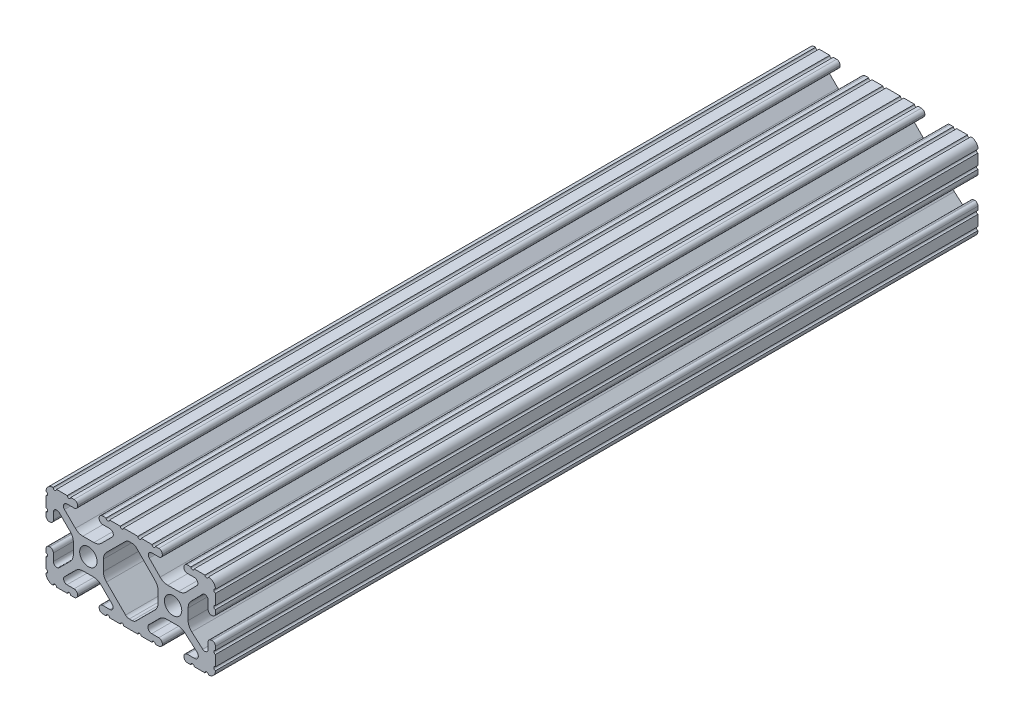
SolidWorks part; units mm, degrees
ref_plane "Front Plane" through (0, 0, 0) normal (0, 0, 1) x (1, 0, 0)
ref_plane "Top Plane" through (0, 0, 0) normal (0, 1, 0) x (1, 0, 0)
ref_plane "Right Plane" through (0, 0, 0) normal (1, 0, 0) x (0, 0, -1)
sketch "Sketch1" plane through (0, 0, 0) normal (0, 0, 1) x (1, 0, 0)
  line L0 (-7.2595, -3.8694) -> (-1.5457, -9.5728)
  line L1 (-8.1915, 1.6223) -> (-8.1915, -1.6223)
  line L2 (-1.504, 9.5765) -> (-7.252, 3.8768)
  line L3 (0.5515, 10.033) -> (-0.3952, 10.033)
  line L4 (7.2829, 3.8459) -> (1.6756, 9.5611)
  line L5 (8.1915, -1.6223) -> (8.1915, 1.6223)
  line L6 (1.5457, -9.5728) -> (7.2595, -3.8694)
  line L7 (-0.4332, -10.033) -> (0.4332, -10.033)
  line L8 (18.0171, 12.7) -> (16.9875, 12.7)
  line L9 (15.9385, 11.651) -> (15.9385, 11.5392)
  line L10 (16.9875, 10.4902) -> (19.1164, 10.4902)
  line L11 (19.8441, 8.7652) -> (16.619, 5.4551)
  line L12 (14.3449, 4.4958) -> (11.0833, 4.4958)
  line L13 (8.817, 5.4472) -> (5.5642, 8.7627)
  line L14 (6.2894, 10.4902) -> (8.4125, 10.4902)
  line L15 (9.4615, 11.5392) -> (9.4615, 11.651)
  line L16 (8.4125, 12.7) -> (7.3829, 12.7)
  line L17 (6.3669, 12.7) -> (3.1496, 12.7)
  line L18 (2.1336, 12.7) -> (-2.1336, 12.7)
  line L19 (-3.1496, 12.7) -> (-6.3669, 12.7)
  line L20 (-7.3829, 12.7) -> (-8.4125, 12.7)
  line L21 (-9.4615, 11.651) -> (-9.4615, 11.5392)
  line L22 (-8.4125, 10.4902) -> (-6.2836, 10.4902)
  line L23 (-5.5326, 8.6661) -> (-8.81, 5.4163)
  line L24 (-11.0455, 4.4958) -> (-14.3545, 4.4958)
  line L25 (-16.59, 5.4163) -> (-19.8674, 8.6661)
  line L26 (-19.1164, 10.4902) -> (-16.9875, 10.4902)
  line L27 (-15.9385, 11.5392) -> (-15.9385, 11.651)
  line L28 (-16.9875, 12.7) -> (-18.0171, 12.7)
  line L29 (-19.0331, 12.7) -> (-22.2504, 12.7)
  line L30 (-25.4, 9.5504) -> (-25.4, 6.3331)
  line L31 (-25.4, 5.3171) -> (-25.4, 4.2375)
  line L32 (-24.401, 3.2385) -> (-24.2392, 3.2385)
  line L33 (-23.1902, 4.2875) -> (-23.1902, 6.3347)
  line L34 (-21.434, 7.0665) -> (-18.148, 3.8082)
  line L35 (-17.2085, 1.5536) -> (-17.2085, -1.6952)
  line L36 (-18.1405, -3.9423) -> (-21.4316, -7.2274)
  line L37 (-23.1902, -6.498) -> (-23.1902, -4.2875)
  line L38 (-24.2392, -3.2385) -> (-24.351, -3.2385)
  line L39 (-25.4, -4.2875) -> (-25.4, -5.3171)
  line L40 (-25.4, -6.3331) -> (-25.4, -9.5504)
  line L41 (-22.2504, -12.7) -> (-19.0331, -12.7)
  line L42 (-18.0171, -12.7) -> (-16.9875, -12.7)
  line L43 (-15.9384, -11.651) -> (-15.9384, -11.5392)
  line L44 (-16.9875, -10.4902) -> (-19.1164, -10.4902)
  line L45 (-19.8341, -8.7551) -> (-16.4966, -5.4237)
  line L46 (-14.2536, -4.4958) -> (-11.1464, -4.4958)
  line L47 (-8.9034, -5.4237) -> (-5.5659, -8.7551)
  line L48 (-6.2836, -10.4902) -> (-8.4125, -10.4902)
  line L49 (-9.4616, -11.5392) -> (-9.4616, -11.651)
  line L50 (-8.4125, -12.7) -> (-7.3829, -12.7)
  line L51 (-6.3669, -12.7) -> (-3.1496, -12.7)
  line L52 (-2.1336, -12.7) -> (2.1336, -12.7)
  line L53 (3.1496, -12.7) -> (6.3669, -12.7)
  line L54 (7.3829, -12.7) -> (8.4125, -12.7)
  line L55 (9.4616, -11.651) -> (9.4616, -11.5392)
  line L56 (8.4125, -10.4902) -> (6.2894, -10.4902)
  line L57 (5.4807, -8.5353) -> (8.5979, -5.4237)
  line L58 (10.8409, -4.4958) -> (14.1026, -4.4958)
  line L59 (16.1879, -5.2766) -> (19.8682, -8.4822)
  line L60 (19.1164, -10.4902) -> (16.9875, -10.4902)
  line L61 (15.9384, -11.5392) -> (15.9384, -11.651)
  line L62 (16.9875, -12.7) -> (18.0171, -12.7)
  line L63 (19.0331, -12.7) -> (22.2504, -12.7)
  line L64 (25.4, -9.5504) -> (25.4, -6.3331)
  line L65 (25.4, -5.3171) -> (25.4, -4.2375)
  line L66 (24.401, -3.2385) -> (24.1892, -3.2385)
  line L67 (23.1902, -4.2375) -> (23.1902, -6.1559)
  line L68 (21.584, -6.8869) -> (18.2982, -4.025)
  line L69 (17.2085, -1.6308) -> (17.2085, 1.6308)
  line L70 (18.1094, 3.8465) -> (21.5263, 7.3534)
  line L71 (23.1902, 6.6769) -> (23.1902, 4.2375)
  line L72 (24.1892, 3.2385) -> (24.401, 3.2385)
  line L73 (25.4, 4.2375) -> (25.4, 5.3171)
  line L74 (25.4, 6.3332) -> (25.4, 9.5504)
  line L75 (22.2504, 12.7) -> (19.0331, 12.7)
  circle A0 centre (-12.7, 0) radius 2.6035
  circle A1 centre (12.7, 0) radius 2.6035
  arc A2 (-1.5457, -9.5728) -> (-0.4332, -10.033) centre (-0.4332, -8.4582) ccw
  arc A3 (-8.1915, -1.6223) -> (-7.2595, -3.8694) centre (-5.0165, -1.6223) ccw
  arc A4 (-7.252, 3.8768) -> (-8.1915, 1.6223) centre (-5.0165, 1.6223) ccw
  arc A5 (-0.3952, 10.033) -> (-1.504, 9.5765) centre (-0.3952, 8.4582) ccw
  arc A6 (1.6756, 9.5611) -> (0.5515, 10.033) centre (0.5515, 8.4582) ccw
  arc A7 (8.1915, 1.6223) -> (7.2829, 3.8459) centre (5.0165, 1.6223) ccw
  arc A8 (7.2595, -3.8694) -> (8.1915, -1.6223) centre (5.0165, -1.6223) ccw
  arc A9 (0.4332, -10.033) -> (1.5457, -9.5728) centre (0.4332, -8.4582) ccw
  arc A10 (18.0171, 12.7) -> (19.0331, 12.7) centre (18.5251, 12.7) ccw
  arc A11 (16.9875, 12.7) -> (15.9385, 11.651) centre (16.9875, 11.651) ccw
  arc A12 (15.9385, 11.5392) -> (16.9875, 10.4902) centre (16.9875, 11.5392) ccw
  arc A13 (19.8441, 8.7652) -> (19.1164, 10.4902) centre (19.1164, 9.4742) ccw
  arc A14 (14.3449, 4.4958) -> (16.619, 5.4551) centre (14.3449, 7.6708) ccw
  arc A15 (8.817, 5.4472) -> (11.0833, 4.4958) centre (11.0833, 7.6708) ccw
  arc A16 (6.2894, 10.4902) -> (5.5642, 8.7627) centre (6.2894, 9.4742) ccw
  arc A17 (8.4125, 10.4902) -> (9.4615, 11.5392) centre (8.4125, 11.5392) ccw
  arc A18 (9.4615, 11.651) -> (8.4125, 12.7) centre (8.4125, 11.651) ccw
  arc A19 (6.3669, 12.7) -> (7.3829, 12.7) centre (6.8749, 12.7) ccw
  arc A20 (2.1336, 12.7) -> (3.1496, 12.7) centre (2.6416, 12.7) ccw
  arc A21 (-3.1496, 12.7) -> (-2.1336, 12.7) centre (-2.6416, 12.7) ccw
  arc A22 (-7.3829, 12.7) -> (-6.3669, 12.7) centre (-6.8749, 12.7) ccw
  arc A23 (-8.4125, 12.7) -> (-9.4615, 11.651) centre (-8.4125, 11.651) ccw
  arc A24 (-9.4615, 11.5392) -> (-8.4125, 10.4902) centre (-8.4125, 11.5392) ccw
  arc A25 (-5.5326, 8.6661) -> (-6.2836, 10.4902) centre (-6.2836, 9.4235) ccw
  arc A26 (-11.0455, 4.4958) -> (-8.81, 5.4163) centre (-11.0455, 7.6708) ccw
  arc A27 (-16.59, 5.4163) -> (-14.3545, 4.4958) centre (-14.3545, 7.6708) ccw
  arc A28 (-19.1164, 10.4902) -> (-19.8674, 8.6661) centre (-19.1164, 9.4235) ccw
  arc A29 (-16.9875, 10.4902) -> (-15.9385, 11.5392) centre (-16.9875, 11.5392) ccw
  arc A30 (-15.9385, 11.651) -> (-16.9875, 12.7) centre (-16.9875, 11.651) ccw
  arc A31 (-19.0331, 12.7) -> (-18.0171, 12.7) centre (-18.5251, 12.7) ccw
  arc A32 (-23.2664, 12.6998) -> (-22.2504, 12.7) centre (-22.7584, 12.7) ccw
  arc A33 (-23.2664, 12.6998) -> (-25.3998, 10.5664) centre (-23.2918, 10.5918) ccw
  arc A34 (-25.4, 9.5504) -> (-25.3998, 10.5664) centre (-25.4, 10.0584) ccw
  arc A35 (-25.4, 5.3171) -> (-25.4, 6.3331) centre (-25.4, 5.8251) ccw
  arc A36 (-25.4, 4.2375) -> (-24.401, 3.2385) centre (-24.401, 4.2375) ccw
  arc A37 (-24.2392, 3.2385) -> (-23.1902, 4.2875) centre (-24.2392, 4.2875) ccw
  arc A38 (-21.434, 7.0665) -> (-23.1902, 6.3347) centre (-22.1596, 6.3347) ccw
  arc A39 (-17.2085, 1.5536) -> (-18.148, 3.8082) centre (-20.3835, 1.5536) ccw
  arc A40 (-18.1405, -3.9423) -> (-17.2085, -1.6952) centre (-20.3835, -1.6952) ccw
  arc A41 (-23.1902, -6.498) -> (-21.4316, -7.2274) centre (-22.1596, -6.498) ccw
  arc A42 (-23.1902, -4.2875) -> (-24.2392, -3.2385) centre (-24.2392, -4.2875) ccw
  arc A43 (-24.351, -3.2385) -> (-25.4, -4.2875) centre (-24.351, -4.2875) ccw
  arc A44 (-25.4, -6.3331) -> (-25.4, -5.3171) centre (-25.4, -5.8251) ccw
  arc A45 (-25.3998, -10.5664) -> (-25.4, -9.5504) centre (-25.4, -10.0584) ccw
  arc A46 (-25.3998, -10.5664) -> (-23.2664, -12.6998) centre (-23.2918, -10.5918) ccw
  arc A47 (-22.2504, -12.7) -> (-23.2664, -12.6998) centre (-22.7584, -12.7) ccw
  arc A48 (-18.0171, -12.7) -> (-19.0331, -12.7) centre (-18.5251, -12.7) ccw
  arc A49 (-16.9875, -12.7) -> (-15.9384, -11.651) centre (-16.9875, -11.651) ccw
  arc A50 (-15.9384, -11.5392) -> (-16.9875, -10.4902) centre (-16.9875, -11.5392) ccw
  arc A51 (-19.8341, -8.7551) -> (-19.1164, -10.4902) centre (-19.1164, -9.4742) ccw
  arc A52 (-14.2536, -4.4958) -> (-16.4966, -5.4237) centre (-14.2536, -7.6708) ccw
  arc A53 (-8.9034, -5.4237) -> (-11.1464, -4.4958) centre (-11.1464, -7.6708) ccw
  arc A54 (-6.2836, -10.4902) -> (-5.5659, -8.7551) centre (-6.2836, -9.4742) ccw
  arc A55 (-8.4125, -10.4902) -> (-9.4616, -11.5392) centre (-8.4125, -11.5392) ccw
  arc A56 (-9.4616, -11.651) -> (-8.4125, -12.7) centre (-8.4125, -11.651) ccw
  arc A57 (-6.3669, -12.7) -> (-7.3829, -12.7) centre (-6.8749, -12.7) ccw
  arc A58 (-2.1336, -12.7) -> (-3.1496, -12.7) centre (-2.6416, -12.7) ccw
  arc A59 (3.1496, -12.7) -> (2.1336, -12.7) centre (2.6416, -12.7) ccw
  arc A60 (7.3829, -12.7) -> (6.3669, -12.7) centre (6.8749, -12.7) ccw
  arc A61 (8.4125, -12.7) -> (9.4616, -11.651) centre (8.4125, -11.651) ccw
  arc A62 (9.4616, -11.5392) -> (8.4125, -10.4902) centre (8.4125, -11.5392) ccw
  arc A63 (5.4807, -8.5353) -> (6.2894, -10.4902) centre (6.2894, -9.3455) ccw
  arc A64 (10.8409, -4.4958) -> (8.5979, -5.4237) centre (10.8409, -7.6708) ccw
  arc A65 (16.1879, -5.2766) -> (14.1026, -4.4958) centre (14.1026, -7.6708) ccw
  arc A66 (19.1164, -10.4902) -> (19.8682, -8.4822) centre (19.1164, -9.3455) ccw
  arc A67 (16.9875, -10.4902) -> (15.9384, -11.5392) centre (16.9875, -11.5392) ccw
  arc A68 (15.9384, -11.651) -> (16.9875, -12.7) centre (16.9875, -11.651) ccw
  arc A69 (19.0331, -12.7) -> (18.0171, -12.7) centre (18.5251, -12.7) ccw
  arc A70 (23.2664, -12.6998) -> (22.2504, -12.7) centre (22.7584, -12.7) ccw
  arc A71 (23.2664, -12.6998) -> (25.3998, -10.5664) centre (23.2918, -10.5918) ccw
  arc A72 (25.4, -9.5504) -> (25.3998, -10.5664) centre (25.4, -10.0584) ccw
  arc A73 (25.4, -5.3171) -> (25.4, -6.3331) centre (25.4, -5.8251) ccw
  arc A74 (25.4, -4.2375) -> (24.401, -3.2385) centre (24.401, -4.2375) ccw
  arc A75 (24.1892, -3.2385) -> (23.1902, -4.2375) centre (24.1892, -4.2375) ccw
  arc A76 (21.584, -6.8869) -> (23.1902, -6.1559) centre (22.2207, -6.1559) ccw
  arc A77 (17.2085, -1.6308) -> (18.2982, -4.025) centre (20.3835, -1.6308) ccw
  arc A78 (18.1094, 3.8465) -> (17.2085, 1.6308) centre (20.3835, 1.6308) ccw
  arc A79 (23.1902, 6.6769) -> (21.5263, 7.3534) centre (22.2207, 6.6769) ccw
  arc A80 (23.1902, 4.2375) -> (24.1892, 3.2385) centre (24.1892, 4.2375) ccw
  arc A81 (24.401, 3.2385) -> (25.4, 4.2375) centre (24.401, 4.2375) ccw
  arc A82 (25.4, 6.3332) -> (25.4, 5.3171) centre (25.4, 5.8251) ccw
  arc A83 (25.3998, 10.5664) -> (25.4, 9.5504) centre (25.4, 10.0584) ccw
  arc A84 (25.3998, 10.5664) -> (23.2664, 12.6998) centre (23.2918, 10.5918) ccw
  arc A85 (22.2504, 12.7) -> (23.2664, 12.6998) centre (22.7584, 12.7) ccw
  point P248 (0, 10.033)
extrude "Boss-Extrude1" add sketch "Sketch1" along normal mid plane 228.6
